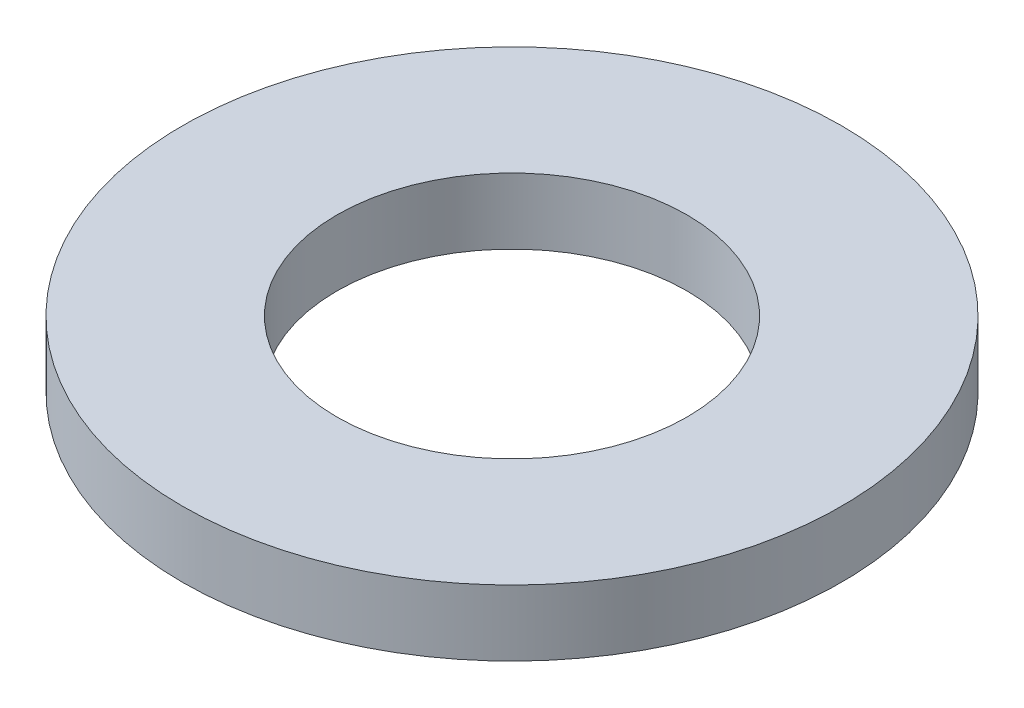
SolidWorks part; units mm, degrees
material "1060 Alloy"
ref_plane "Front Plane" through (0, 0, 0) normal (0, 0, 1) x (1, 0, 0)
ref_plane "Top Plane" through (0, 0, 0) normal (0, 1, 0) x (1, 0, 0)
ref_plane "Right Plane" through (0, 0, 0) normal (1, 0, 0) x (0, 0, -1)
sketch "Sketch1" plane through (0, 0, 0) normal (0, 1, 0) x (1, 0, 0)
  circle A0 centre (0, 0) radius 3.3734
  circle A1 centre (0, 0) radius 6.35
  dimension "D1" = 6.7469
  dimension "D2" = 12.7
extrude "Boss-Extrude1" add sketch "Sketch1" along normal blind 1.27
